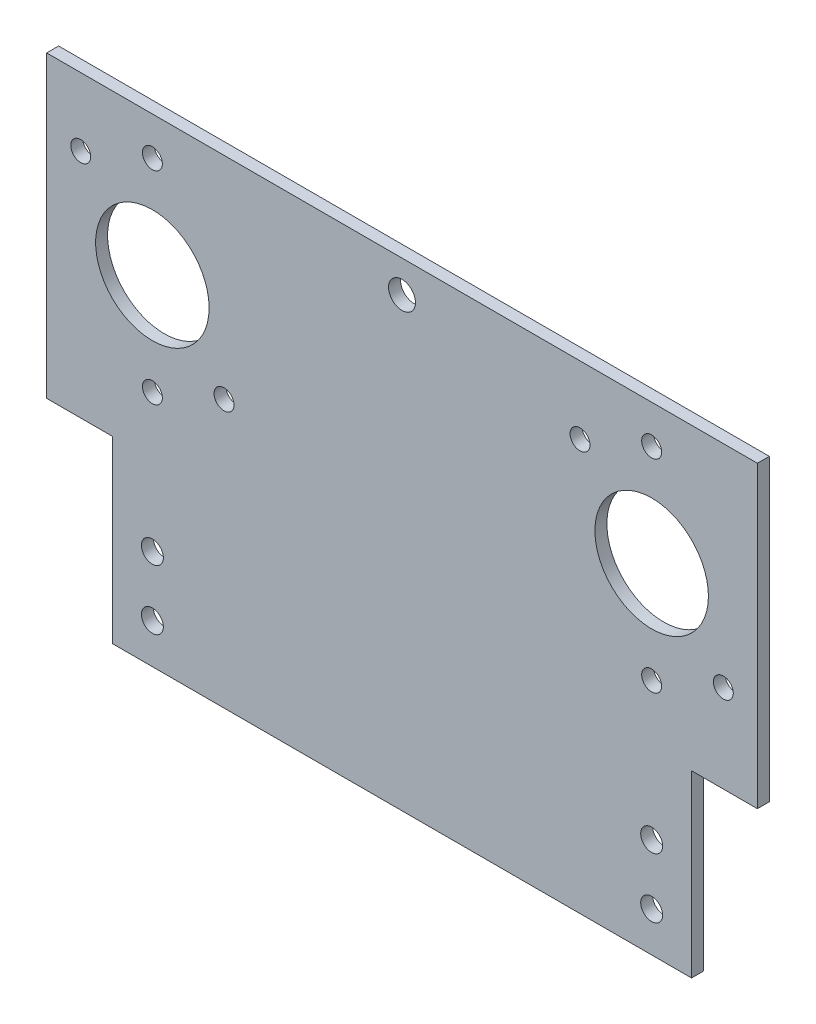
SolidWorks part; units mm, degrees
ref_plane "Front Plane" through (0, 0, 0) normal (0, 0, 1) x (1, 0, 0)
ref_plane "Top Plane" through (0, 0, 0) normal (0, 1, 0) x (1, 0, 0)
ref_plane "Right Plane" through (0, 0, 0) normal (1, 0, 0) x (0, 0, -1)
sketch "Sketch1" plane through (0, 0, 0) normal (0, 0, 1) x (1, 0, 0)
  line L1 (0, 0) -> (178.16, 0)
  line L2 (0, 0) -> (0, -120)
  line L3 (0, -120) -> (178.16, -120)
  line L4 (178.16, 0) -> (178.16, -120)
  dimension "D1" = 120
  dimension "D2" = 178.16
extrude "Boss-Extrude1" add sketch "Sketch1" along normal blind 3
sketch "Sketch2" plane through (0, 0, 3) normal (0, 0, 1) x (1, 0, 0)
  line L0 (0, 0) -> (0, -120) construction
  line L1 (178.16, -120) -> (178.16, 0) construction
  line L2 (0, -120) -> (178.16, -120) construction
  line L3 (178.16, 0) -> (0, 0) construction
  circle A0 centre (26.5, -35) radius 14.225
  circle A1 centre (151.66, -35) radius 14.225
  circle A2 centre (26.5, -110) radius 2.75
  circle A5 centre (151.66, -110) radius 2.75
  circle A7 centre (89.08, -8) radius 3.375
  circle A8 centre (26.5, -95) radius 2.75
  circle A9 centre (151.66, -95) radius 2.75
  point P9 (89.08, 0)
  dimension "D1" = 28.45
  dimension "D2" = 28.45
  dimension "D3" = 5.5
  dimension "D4" = 35
  dimension "D5" = 6.75
  dimension "D6" = 5.5
  dimension "D7" = 15
  dimension "D8" = 5.5
  dimension "D11" = 5.5
  dimension "D9" = 26.5
  dimension "D10" = 26.5
  dimension "D13" = 15
  dimension "D14" = 10
  dimension "D16" = 8
extrude "Cut-Extrude1" cut sketch "Sketch2" against normal through all
sketch "Sketch3" plane through (0, 0, 0) normal (0, 0, -1) x (-1, 0, 0)
  circle A0 centre (-44.4605, -52.9605) radius 2.0193 construction
  circle A1 centre (-26.5, -9.6) radius 2.0193 construction
  circle A2 centre (-8.5395, -17.0395) radius 2.0193 construction
  circle A3 centre (-44.4605, -52.9605) radius 2.0193
  circle A4 centre (-26.5, -9.6) radius 2.0193
  circle A5 centre (-8.5395, -17.0395) radius 2.0193
  circle A6 centre (-26.5, -60.4) radius 2.0193 construction
  circle A7 centre (-26.5, -60.4) radius 2.0193
  circle A8 centre (-133.6995, -17.0395) radius 2.0193 construction
  circle A9 centre (-151.66, -9.6) radius 2.0193 construction
  circle A10 centre (-133.6995, -17.0395) radius 2.0193
  circle A11 centre (-151.66, -9.6) radius 2.0193
  circle A12 centre (-151.66, -60.4) radius 2.0193 construction
  circle A13 centre (-169.6205, -52.9605) radius 2.0193 construction
  circle A14 centre (-151.66, -60.4) radius 2.0193
  circle A15 centre (-169.6205, -52.9605) radius 2.0193
  point P25 (-26.5, -60.4)
  point P26 (-44.4605, -52.9605)
  point P27 (-26.5, -9.6)
  point P28 (-8.5395, -17.0395)
  point P29 (-151.66, -60.4)
  point P30 (-169.6205, -52.9605)
  point P31 (-151.66, -9.6)
  point P32 (-133.6995, -17.0395)
extrude "Cut-Extrude2" cut sketch "Sketch3" against normal through all
sketch "Sketch6" plane through (0, 0, 3) normal (0, 0, 1) x (1, 0, 0)
  circle A0 centre (26.5, -60.4) radius 2.5
  circle A1 centre (44.4605, -52.9605) radius 2.5
  circle A3 centre (26.5, -9.6) radius 2.5
  circle A4 centre (8.5395, -17.0395) radius 2.5
  circle A5 centre (169.6205, -52.9605) radius 2.5
  circle A6 centre (151.66, -60.4) radius 2.5
  circle A7 centre (133.6995, -17.0395) radius 2.5
  circle A8 centre (151.66, -9.6) radius 2.5
  dimension "D1" = 5
  dimension "D2" = 5
  dimension "D3" = 5
  dimension "D4" = 5
  dimension "D5" = 5
  dimension "D6" = 5
  dimension "D7" = 5
  dimension "D8" = 5
extrude "Cut-Extrude3" cut sketch "Sketch6" against normal through all
sketch "Sketch7" plane through (0, 0, 3) normal (0, 0, 1) x (1, 0, 0)
  line L1 (178.16, -120) -> (161.66, -120)
  line L2 (178.16, -120) -> (178.16, -75)
  line L3 (178.16, -75) -> (161.66, -75)
  line L4 (161.66, -120) -> (161.66, -75)
  line L5 (0, -120) -> (16.5, -120)
  line L6 (0, -120) -> (0, -75)
  line L7 (0, -75) -> (16.5, -75)
  line L8 (16.5, -120) -> (16.5, -75)
  dimension "D1" = 16.5
  dimension "D2" = 16.5
  dimension "D3" = 45
  dimension "D4" = 45
extrude "Cut-Extrude4" cut sketch "Sketch7" against normal through all
